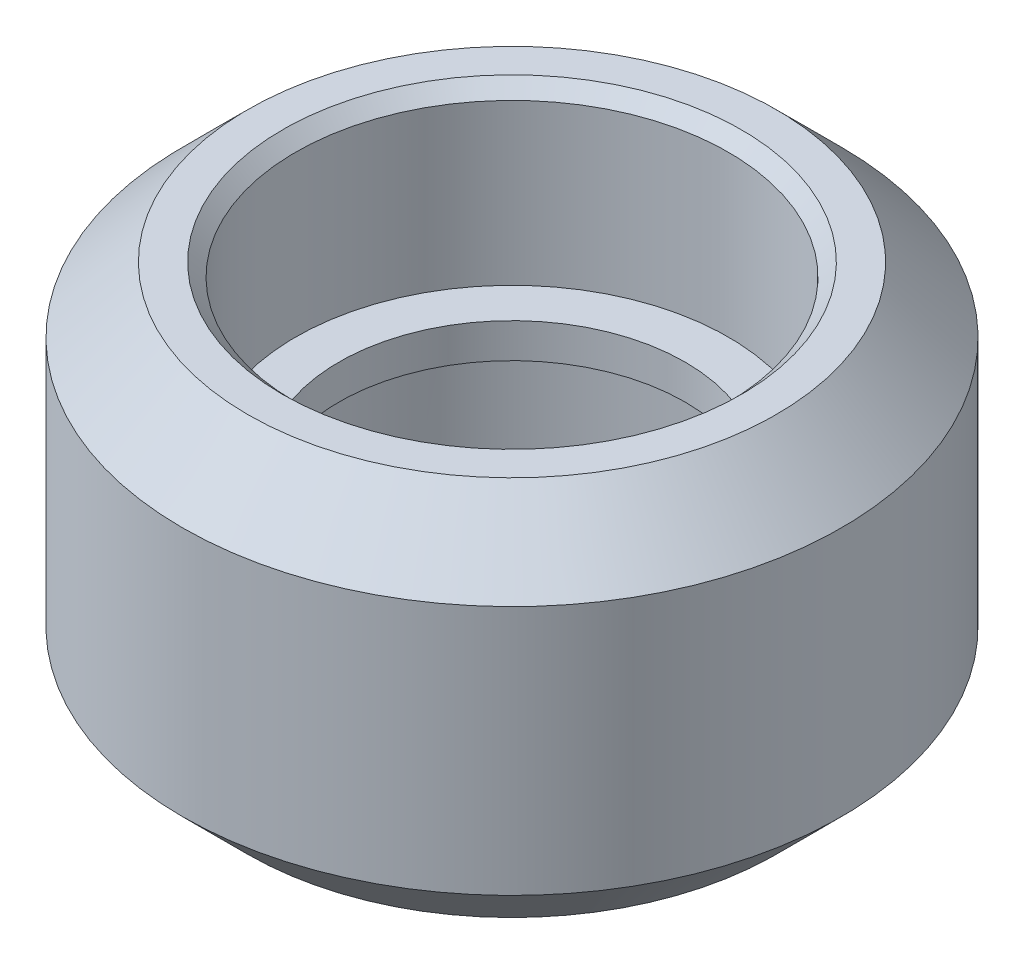
SolidWorks part; units mm, degrees
ref_plane "Front Plane" through (0, 0, 0) normal (0, 0, 1) x (1, 0, 0)
ref_plane "Top Plane" through (0, 0, 0) normal (0, 1, 0) x (1, 0, 0)
ref_plane "Right Plane" through (0, 0, 0) normal (1, 0, 0) x (0, 0, -1)
sketch "Sketch1" plane through (0, 0, 0) normal (0, 1, 0) x (1, 0, 0)
  circle A0 centre (0, 0) radius 7.615
  circle A1 centre (0, 0) radius 4
  point P3 (0, 0)
  dimension "D1" = 8
  dimension "D2" = 15.23
extrude "Boss-Extrude1" add sketch "Sketch1" along normal blind 8.8
sketch "Sketch2" plane through (0, 8.8, 0) normal (0, 1, 0) x (1, 0, 0)
  circle A0 centre (0, 0) radius 5
  dimension "D1" = 10
extrude "Cut-Extrude1" cut sketch "Sketch2" against normal blind 4
sketch "Sketch3" plane through (0, 0, 0) normal (0, -1, 0) x (1, 0, 0)
  circle A0 centre (0, 0) radius 5
  dimension "D1" = 10
extrude "Cut-Extrude2" cut sketch "Sketch3" against normal blind 4
chamfer "Chamfer1" distance 0.3 angle 45 2 edges at (0, 8.8, 5) (0, 0, -5)
chamfer "Chamfer2" distance 1.51 angle 45 2 edges at (0, 8.8, 7.615) (0, 0, 7.615)
